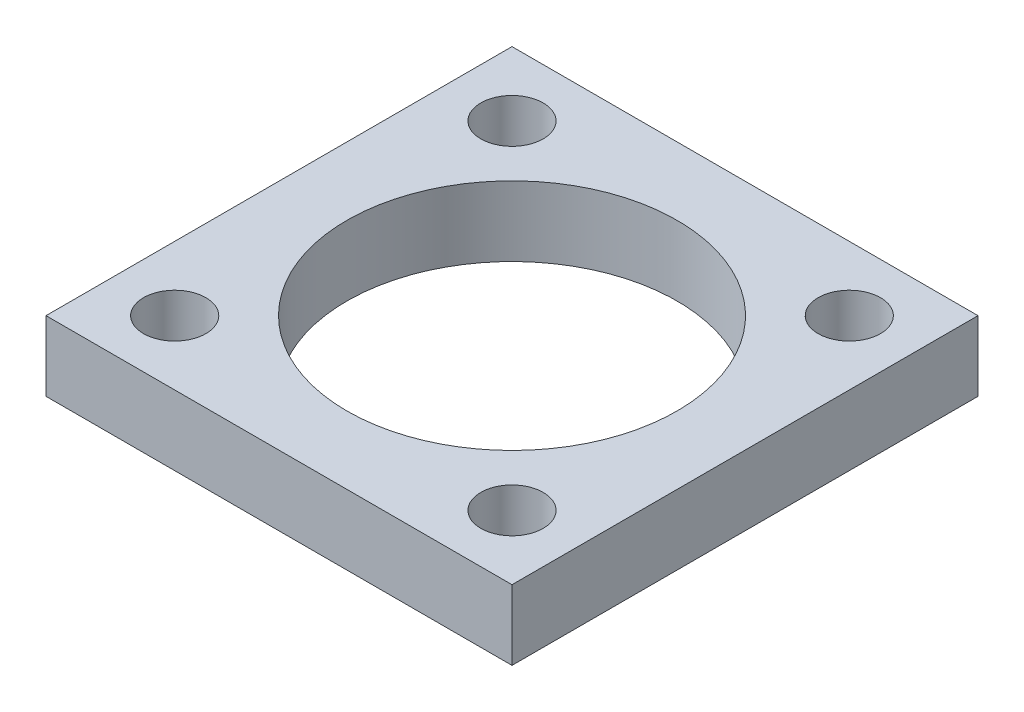
SolidWorks part; units mm, degrees
ref_plane "Front Plane" through (0, 0, 0) normal (0, 0, 1) x (1, 0, 0)
ref_plane "Top Plane" through (0, 0, 0) normal (0, 1, 0) x (1, 0, 0)
ref_plane "Right Plane" through (0, 0, 0) normal (1, 0, 0) x (0, 0, -1)
sketch "Sketch2" plane through (0, 0, 0) normal (0, 1, 0) x (1, 0, 0)
  line L1 (-12.7, -12.7) -> (12.7, -12.7)
  line L2 (-12.7, -12.7) -> (-12.7, 12.7)
  line L3 (-12.7, 12.7) -> (12.7, 12.7)
  line L4 (12.7, -12.7) -> (12.7, 12.7)
  line L5 (-12.7, -12.7) -> (12.7, 12.7) construction
  line L6 (-12.7, 12.7) -> (12.7, -12.7) construction
  point P0 (0, 0)
  dimension "D2" = 25.4
extrude "Boss-Extrude1" add sketch "Sketch2" along normal blind 3.81
sketch "Sketch4" plane through (0, 3.81, 0) normal (0, 1, 0) x (1, 0, 0)
  line L0 (-9.1924, 9.1924) -> (9.1924, -9.1924) construction
  line L1 (-9, 0) -> (9, 0) construction
  line L2 (9.1924, 9.1924) -> (-9.1924, -9.1924) construction
  circle A0 centre (0, 0) radius 9
  point P9 (0, 0)
  point P10 (9.1924, 9.1924)
  point P11 (-9.1924, -9.1924)
  dimension "D3" = 18
  dimension "D1" = 26
  dimension "D2" = 45
  dimension "D4" = 45
extrude "Cut-Extrude1" cut sketch "Sketch4" against normal through all
hole_wizard "M3 Clearance Hole2" positions "3DSketch5" profile "Sketch9" hole size "M3" standard "ANSI Metric" end condition through all
sketch3d "3DSketch5"
  point P0 (-9.1924, 3.81, -9.1924)
  point P3 (9.1924, 3.81, 9.1924)
  point P6 (9.1924, 3.81, -9.1924)
  point P9 (-9.1924, 3.81, 9.1924)
sketch "Sketch9" plane through (-9.1924, 3.81, -9.1924) normal (1, 0, 0) x (0, 0, 1)
  line L0 (0, 0) -> (0, 3.81)
  line L1 (0, 3.81) -> (1.7, 3.81)
  line L2 (1.7, 3.81) -> (1.7, 0)
  line L5 (1.7, 0) -> (0, 0)
  line L11 (0, -6.35) -> (0, 107.95) construction
  dimension "Thru Hole Dia." = 3.4
  dimension "Thru Hole Depth" = 3.81
